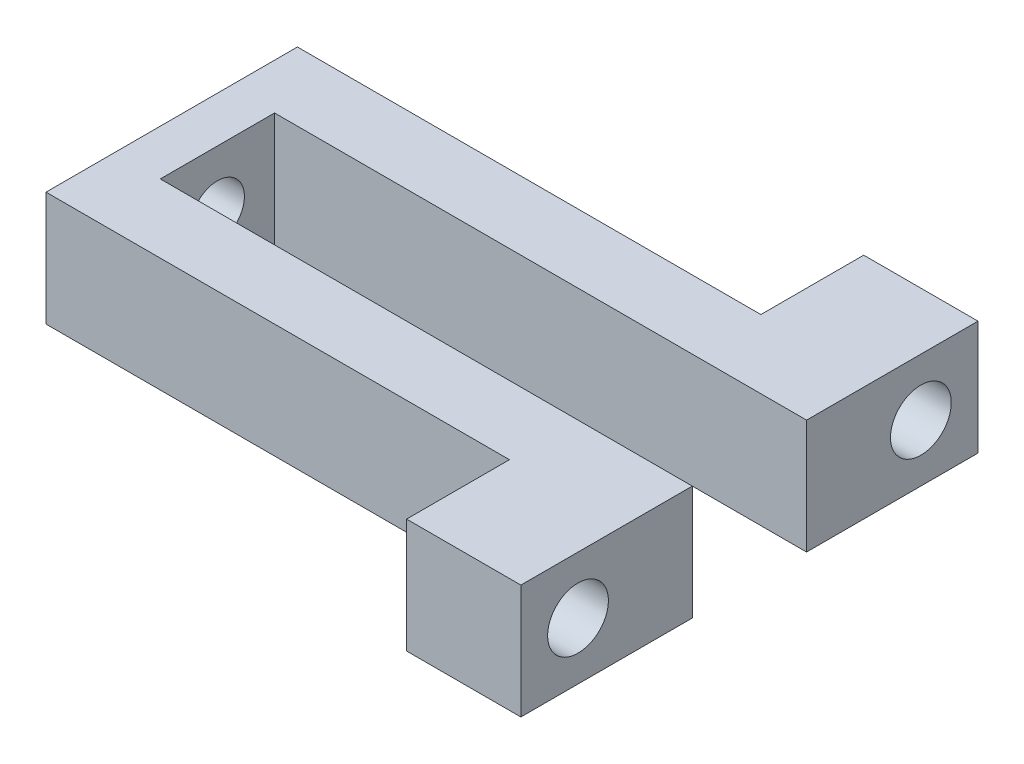
SolidWorks part; units mm, degrees
ref_plane "Front Plane" through (0, 0, 0) normal (0, 0, 1) x (1, 0, 0)
ref_plane "Top Plane" through (0, 0, 0) normal (0, 1, 0) x (1, 0, 0)
ref_plane "Right Plane" through (0, 0, 0) normal (1, 0, 0) x (0, 0, -1)
sketch "Sketch1" plane through (0, 0, 0) normal (0, 1, 0) x (1, 0, 0)
  line L1 (32.1, 25.4) -> (-32.1, 25.4)
  line L2 (32.1, 25.4) -> (32.1, -25.4)
  line L3 (32.1, -25.4) -> (-32.1, -25.4)
  line L4 (-32.1, 25.4) -> (-32.1, -25.4)
  line L5 (32.1, 25.4) -> (-32.1, -25.4) construction
  line L6 (32.1, -25.4) -> (-32.1, 25.4) construction
  point P0 (0, 0)
  dimension "D1" = 50.8
  dimension "D2" = 64.2
extrude "Boss-Extrude1" add sketch "Sketch1" along normal blind 12.7
ref_plane "Plane1" through (0, 0, 0) normal (0, 0, 1) x (1, 0, 0)
sketch "Sketch4" plane through (0, 12.7, 0) normal (0, 1, 0) x (1, 0, 0)
  line L0 (-6.985, 0) -> (6.985, 0) construction
  line L1 (-32.1, -25.4) -> (19.4, -25.4)
  line L2 (-32.1, -25.4) -> (-32.1, -13.97)
  line L3 (-32.1, -13.97) -> (19.4, -13.97)
  line L4 (19.4, -25.4) -> (19.4, -13.97)
  line L5 (-32.1, 13.97) -> (19.4, 13.97)
  line L6 (19.4, 25.4) -> (19.4, 13.97)
  line L7 (-32.1, 25.4) -> (19.4, 25.4)
  line L8 (-32.1, 25.4) -> (-32.1, 13.97)
  line L9 (32.1, -25.4) -> (32.1, 25.4) construction
  line L10 (32.1, -6.35) -> (-27.02, -6.35)
  line L11 (32.1, -6.35) -> (32.1, 6.35)
  line L12 (32.1, 6.35) -> (-27.02, 6.35)
  line L13 (-27.02, -6.35) -> (-27.02, 6.35)
  line L14 (-32.1, 25.4) -> (-32.1, -25.4) construction
  dimension "D1" = 12.7
  dimension "D2" = 12.7
  dimension "D3" = 5.08
  dimension "D4" = 7.62
  dimension "D5" = 7.62
extrude "Cut-Extrude1" cut sketch "Sketch4" against normal blind 12.7
ref_plane "Plane2" through (0, 0, 0) normal (0, 0, 1) x (1, 0, 0)
ref_plane "Plane3" through (0, 6.35, 0) normal (0, 1, 0) x (1, 0, 0)
hole_wizard "CBORE for 1/4 Socket Head Cap Screw1" positions "Sketch5" profile "Sketch6" counterbore size "1/4" standard "ANSI Inch"
sketch "Sketch5" plane through (19.4, 0, 0) normal (-1, 0, 0) x (0, 0, 1)
  line L2 (0, -6.985) -> (0, 6.985) construction
  line L3 (27.94, 6.35) -> (-27.94, 6.35) construction
  point P0 (19.05, 6.35)
  point P12 (-19.05, 6.35)
  dimension "D1" = 38.1
  dimension "D2" = 0
sketch "Sketch6" plane through (19.4, 6.35, 19.05) normal (0, 1, 0) x (0, 0, 1)
  line L0 (0, 0) -> (0, 12.7)
  line L1 (0, 12.7) -> (3.3782, 12.7)
  line L3 (3.3782, 12.7) -> (3.3782, 6.35)
  line L4 (3.3782, 6.35) -> (5.5562, 6.35)
  line L5 (5.5562, 6.35) -> (5.5562, 0)
  line L7 (5.5562, 0) -> (0, 0)
  line L11 (0, -6.35) -> (0, 107.95) construction
  dimension "Thru Hole Dia." = 6.7564
  dimension "Thru Hole Depth" = 12.7
  dimension "C'Bore Dia." = 11.1125
  dimension "C'Bore Depth" = 6.35
hole_wizard "Ø6.0mm Dowel Hole1" positions "Sketch7" profile "Sketch8" hole size "Ø6.0" standard "ANSI Metric" end condition through all
sketch "Sketch7" plane through (-32.1, 0, 0) normal (-1, 0, 0) x (0, 0, 1)
  line L0 (27.94, 6.35) -> (-27.94, 6.35) construction
  point P0 (0, 6.35)
  dimension "D1" = 0
sketch "Sketch8" plane through (-32.1, 6.35, 0) normal (0, 1, 0) x (0, 0, 1)
  line L0 (0, 0) -> (0, 64.2)
  line L1 (0, 64.2) -> (3, 64.2)
  line L2 (3, 64.2) -> (3, 0)
  line L5 (3, 0) -> (0, 0)
  line L11 (0, -6.35) -> (0, 107.95) construction
  dimension "Thru Hole Dia." = 6
  dimension "Thru Hole Depth" = 64.2
